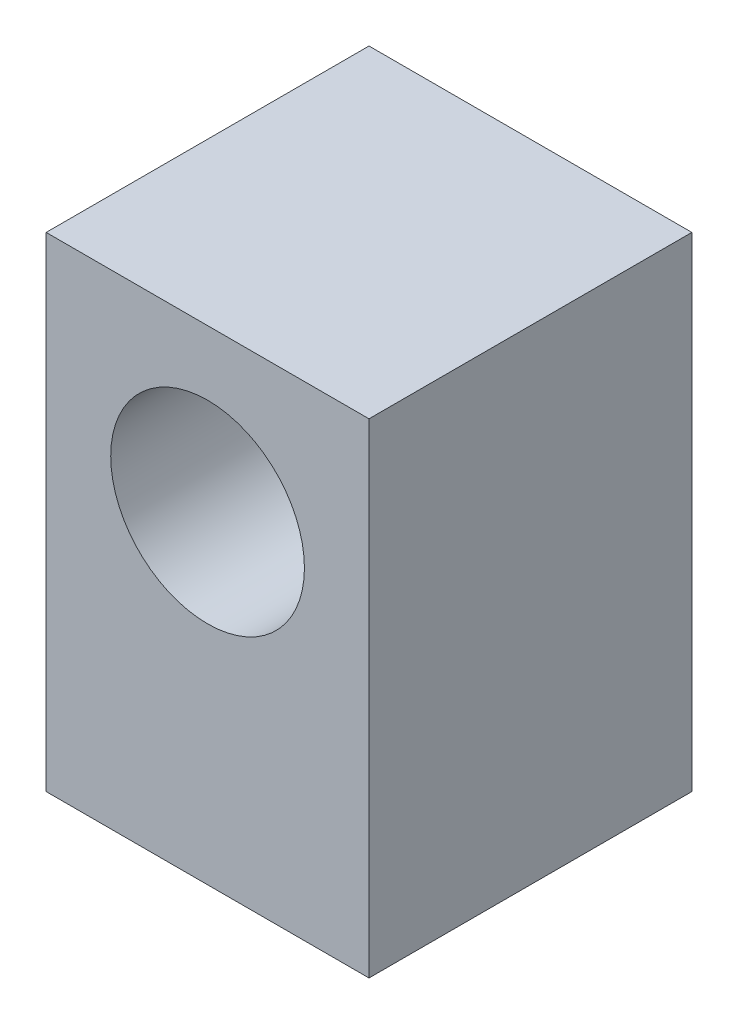
SolidWorks part; units mm, degrees
ref_plane "Front Plane" through (0, 0, 0) normal (0, 0, 1) x (1, 0, 0)
ref_plane "Top Plane" through (0, 0, 0) normal (0, 1, 0) x (1, 0, 0)
ref_plane "Right Plane" through (0, 0, 0) normal (1, 0, 0) x (0, 0, -1)
sketch "Sketch1" plane through (0, 0, 0) normal (0, 1, 0) x (1, 0, 0)
  line L1 (-10, 10) -> (10, 10)
  line L2 (-10, 10) -> (-10, -10)
  line L3 (-10, -10) -> (10, -10)
  line L4 (10, 10) -> (10, -10)
  line L5 (-10, 10) -> (10, -10) construction
  line L6 (-10, -10) -> (10, 10) construction
  point P0 (0, 0)
  dimension "D1" = 20
  dimension "20" = 20
extrude "Boss-Extrude2" add sketch "Sketch1" along normal blind 30
sketch "Sketch2" plane through (0, 0, 10) normal (0, 0, 1) x (1, 0, 0)
  circle A0 centre (0, 20) radius 6
extrude "Cut-Extrude1" cut sketch "Sketch2" against normal up to next
